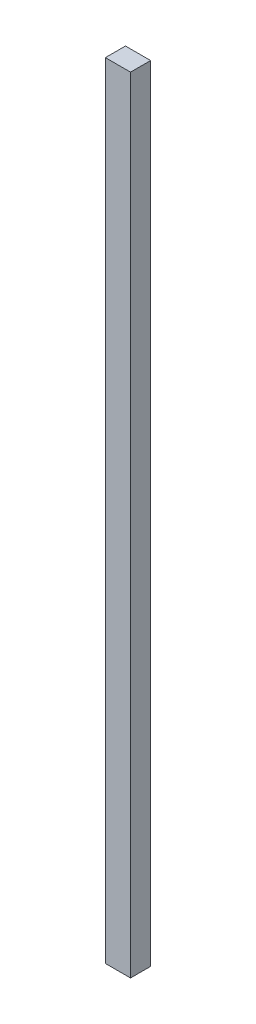
SolidWorks part; units mm, degrees
ref_plane "Спереди" through (0, 0, 0) normal (0, 0, 1) x (1, 0, 0)
ref_plane "Сверху" through (0, 0, 0) normal (0, 1, 0) x (1, 0, 0)
ref_plane "Справа" through (0, 0, 0) normal (1, 0, 0) x (0, 0, -1)
sketch "Эскиз1" plane through (0, 0, 0) normal (0, 1, 0) x (1, 0, 0)
  line L1 (0, 0) -> (25, 0)
  line L2 (0, 0) -> (0, 20)
  line L3 (0, 20) -> (25, 20)
  line L4 (25, 0) -> (25, 20)
extrude "Бобышка-Вытянуть1" add sketch "Эскиз1" along normal blind 780
